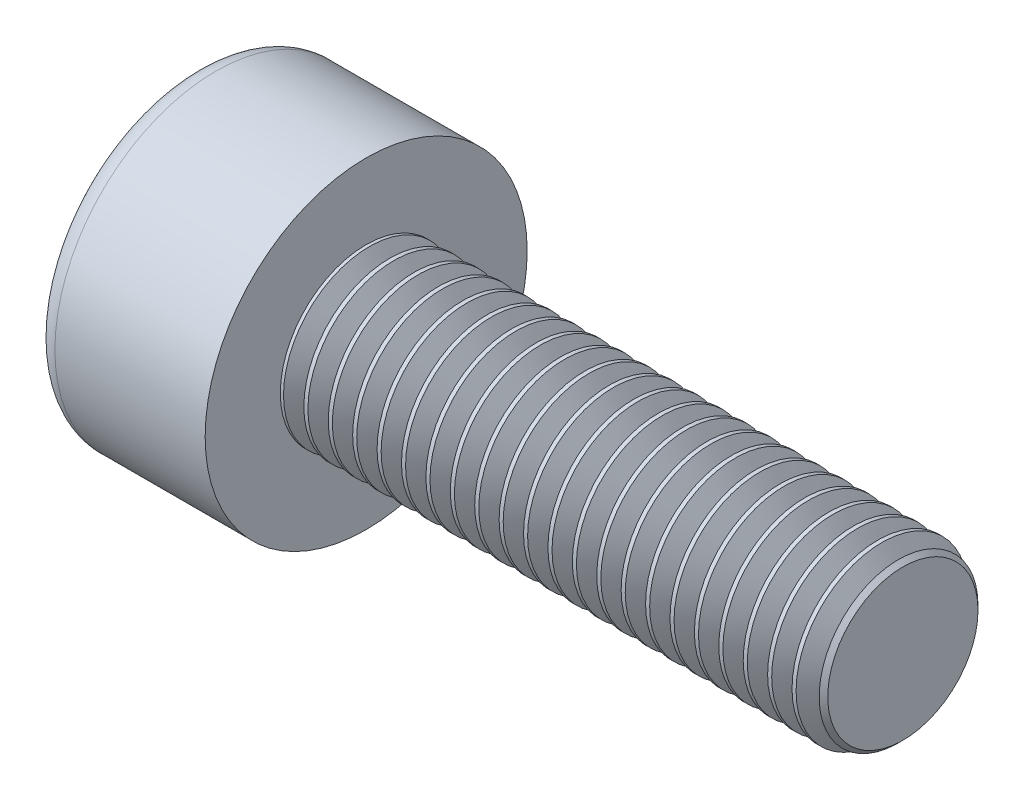
SolidWorks part; units mm, degrees
ref_plane "Front" through (0, 0, 0) normal (0, 0, 1) x (1, 0, 0)
ref_plane "Top" through (0, 0, 0) normal (0, 1, 0) x (1, 0, 0)
ref_plane "Right" through (0, 0, 0) normal (1, 0, 0) x (0, 0, -1)
sketch "Sketch1" plane through (0, 0, 0) normal (1, 0, 0) x (0, 0, -1)
  circle A0 centre (0, 0) radius 1.5
  dimension "dk" = 3
extrude "BaseHead" add sketch "Sketch1" along normal blind 1.6
sketch "Sketch2" plane through (1.6, 0, 0) normal (1, 0, 0) x (0, 0, -1)
  circle A0 centre (0, 0) radius 0.8
  dimension "d" = 1.6
extrude "BaseBody" add sketch "Sketch2" along normal blind 5
cosmetic thread "ThreadCosmetic1" [suppressed] parameters "b"=5, "D2"=1.221
sketch "Sketch3" plane through (0, 0, 0) normal (1, 0, 0) x (0, 0, -1)
  line L1 (0.866, 0) -> (0.433, 0.75)
  line L2 (0.433, 0.75) -> (-0.433, 0.75)
  line L3 (-0.433, 0.75) -> (-0.866, 0)
  line L4 (-0.866, 0) -> (-0.433, -0.75)
  line L5 (-0.433, -0.75) -> (0.433, -0.75)
  line L6 (0.433, -0.75) -> (0.866, 0)
  circle A0 centre (0, 0) radius 0.75 construction
  dimension "s" = 1.5
  dimension "e" = 1.7321
extrude "HexagonSocket" cut sketch "Sketch3" along normal blind 0.7
sketch "Sketch4" plane through (-4.1961, 0.75, 0) normal (0, 0, 1) x (-1, 0, 0)
  line L0 (-4.8961, 1.5) -> (-5.3292, 0.75)
  line L2 (-5.3292, 0.75) -> (-4.8961, 0.75)
  line L3 (-4.8961, 0.75) -> (-4.8961, 1.5)
  line L4 (-5.0351, 0.75) -> (0.839, 0.75) construction
  line L5 (-10.7961, 0.75) -> (-5.7961, 0.75) construction
  line L6 (-5.7961, 0.75) -> (-4.1961, 0.75) construction
  dimension "m" = 60
revolve "Cut-Revolve1" cut sketch "Sketch4" angle 360 about L4
fillet "HeadFillet" [suppressed] radius 0.1
fillet "TopFillet" radius 0.2 1 edges at (0, 0, -1.5)
chamfer "Chamfer1" distance 0.1 angle 45 1 edges at (6.6, 0, -0.8)
sketch "Sketch5" plane through (0, 0, 0) normal (0, 0, 1) x (1, 0, 0)
  line L0 (6.5, 0.6359) -> (6.5947, 0.8)
  line L1 (6.5947, 0.8) -> (6.5947, 0.9895)
  line L2 (6.5947, 0.9895) -> (6.4053, 0.9895)
  line L3 (6.4053, 0.9895) -> (6.4053, 0.8)
  line L4 (6.4053, 0.8) -> (6.5, 0.6359)
  line L5 (0, 0) -> (7.8886, 0) construction
  line L6 (6.5, -0.8) -> (6.5, 0.8) construction
  dimension "D1" = 1.6
  dimension "D2" = 0.1895
revolve "Cut-Revolve10" cut sketch "Sketch5" angle 360 about L5
pattern_linear "LPattern10" count 22 spacing 0.2274 along (-1, 0, 0) of "Cut-Revolve10"
equation "\"r1@TopFillet\" = \"d@Sketch2\" / 8"
equation "\"D1@Chamfer1\" = \"r@HeadFillet\""
equation "\"D1@Sketch5\" = \"d@Sketch2\""
equation "\"D2@Sketch5\" =  ( \"d@Sketch2\" - \"D2@ThreadCosmetic1\" )  / 2"
equation "\"D3@LPattern10\" = \"D2@Sketch5\" * 1.2"
equation "\"D1@LPattern10\" = \"b@ThreadCosmetic1\" / \"D3@LPattern10\""
